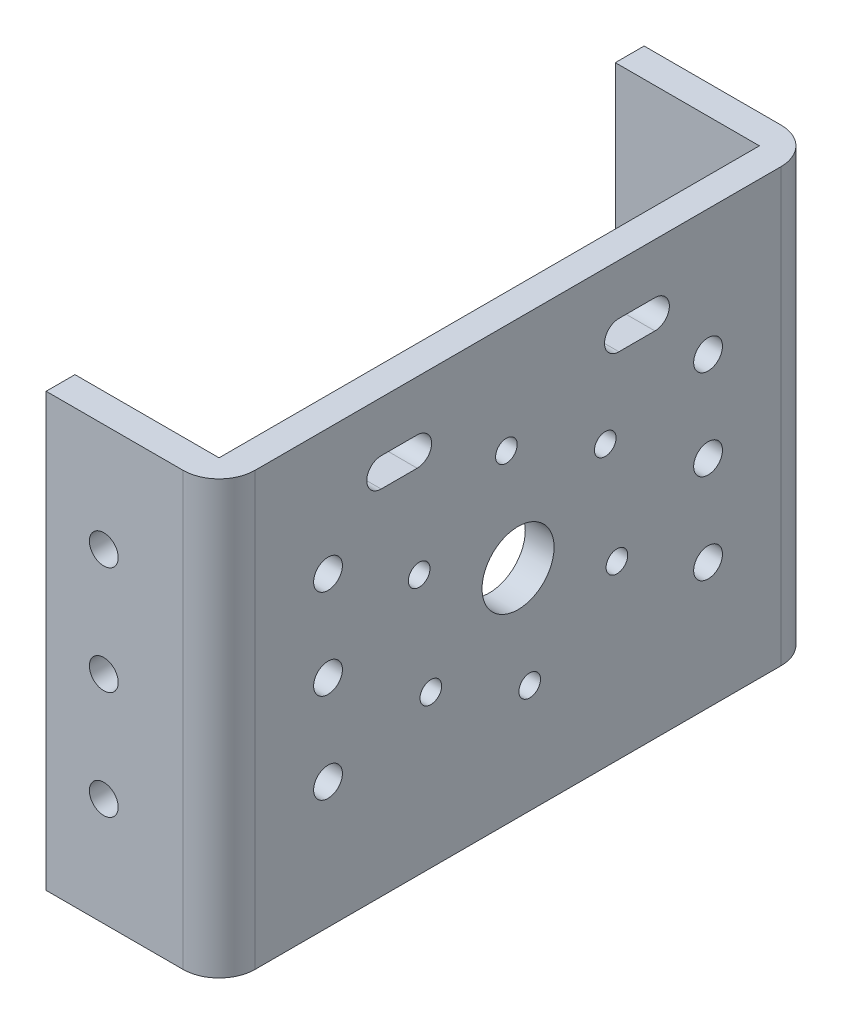
SolidWorks part; units mm, degrees
ref_plane "Front Plane" through (0, 0, 0) normal (0, 0, 1) x (1, 0, 0)
ref_plane "Top Plane" through (0, 0, 0) normal (0, 1, 0) x (1, 0, 0)
ref_plane "Right Plane" through (0, 0, 0) normal (1, 0, 0) x (0, 0, -1)
sketch "Sketch1" plane through (0, 0, 0) normal (1, 0, 0) x (0, 0, -1)
  line L1 (41.5, -30) -> (-41.5, -30)
  line L2 (41.5, -30) -> (41.5, 30)
  line L3 (41.5, 30) -> (-41.5, 30)
  line L4 (-41.5, -30) -> (-41.5, 30)
  line L5 (41.5, -30) -> (-41.5, 30) construction
  line L6 (41.5, 30) -> (-41.5, -30) construction
  point P0 (0, 0)
  dimension "D1" = 83
  dimension "D2" = 60
extrude "Boss-Extrude1" add sketch "Sketch1" along normal blind 4
sketch "Sketch2" plane through (4, 0, 0) normal (1, 0, 0) x (0, 0, -1)
  circle A0 centre (0, 0) radius 5
extrude "Cut-Extrude1" cut sketch "Sketch2" against normal through all
sketch "Sketch4" plane through (4, 0, 0) normal (1, 0, 0) x (0, 0, -1)
  circle A0 centre (-13.7237, 6.0548) radius 1.5
  circle A1 centre (-12.1055, -8.8576) radius 1.5
  circle A2 centre (1.6182, -14.9125) radius 1.5
  circle A3 centre (13.7237, -6.0548) radius 1.5
  circle A4 centre (12.1055, 8.8576) radius 1.5
  circle A5 centre (-1.6182, 14.9125) radius 1.5
extrude "Cut-Extrude2" cut sketch "Sketch4" against normal blind 10
sketch "Sketch6" plane through (4, 0, 0) normal (1, 0, 0) x (0, 0, -1)
  circle A0 centre (-26.375, 12.5) radius 2
  circle A1 centre (-26.375, 0) radius 2
  circle A2 centre (-26.375, -12.5) radius 2
  circle A3 centre (26.375, 12.5) radius 2
  circle A4 centre (26.375, 0) radius 2
  circle A5 centre (26.375, -12.5) radius 2
extrude "Cut-Extrude3" cut sketch "Sketch6" against normal blind 10
sketch "Sketch7" plane through (4, 0, 0) normal (1, 0, 0) x (0, 0, -1)
  line L0 (-19, 21) -> (-14, 21) construction
  line L1 (-19, 23) -> (-14, 23)
  line L2 (-19, 19) -> (-14, 19)
  line L3 (0, 30) -> (0, -30) construction
  line L4 (41.5, 30) -> (-41.5, 30) construction
  line L5 (-41.5, -30) -> (41.5, -30) construction
  line L6 (19, 21) -> (14, 21) construction
  line L7 (19, 23) -> (14, 23)
  line L8 (19, 19) -> (14, 19)
  arc A0 (-19, 23) -> (-19, 19) centre (-19, 21) ccw
  arc A1 (-14, 19) -> (-14, 23) centre (-14, 21) ccw
  arc A2 (19, 23) -> (19, 19) centre (19, 21) cw
  arc A3 (14, 19) -> (14, 23) centre (14, 21) cw
  point P2 (-16.5, 21)
  point P15 (16.5, 21)
  dimension "D1" = 2
  dimension "D2" = 5
  dimension "D3" = 14
  dimension "D4" = 9
extrude "Cut-Extrude4" cut sketch "Sketch7" against normal blind 10
sketch "Sketch8" plane through (0, 0, 0) normal (-1, 0, 0) x (0, 0, 1)
  line L0 (41.5, -30) -> (-41.5, -30) construction
  line L1 (-41.5, 30) -> (-37.5, 30)
  line L2 (-41.5, 30) -> (-41.5, -30)
  line L3 (-41.5, -30) -> (-37.5, -30)
  line L4 (-37.5, 30) -> (-37.5, -30)
  line L5 (-37.5, 30) -> (-37.5, -30) construction
  line L7 (41.5, 30) -> (37.5, 30)
  line L8 (41.5, 30) -> (41.5, -30)
  line L9 (41.5, -30) -> (37.5, -30)
  line L10 (37.5, 30) -> (37.5, -30)
  dimension "D1" = 4
extrude "Boss-Extrude2" add sketch "Sketch8" along normal blind 20
fillet "Fillet1" radius 5 2 edges at (4, 0, 41.5) (4, 0, -41.5)
sketch "Sketch10" plane through (0, 0, 41.5) normal (0, 0, 1) x (1, 0, 0)
  circle A0 centre (-12, 15) radius 2
  circle A1 centre (-12, 0) radius 2
  circle A2 centre (-12, -15) radius 2
extrude "Cut-Extrude5" cut sketch "Sketch10" against normal through all
